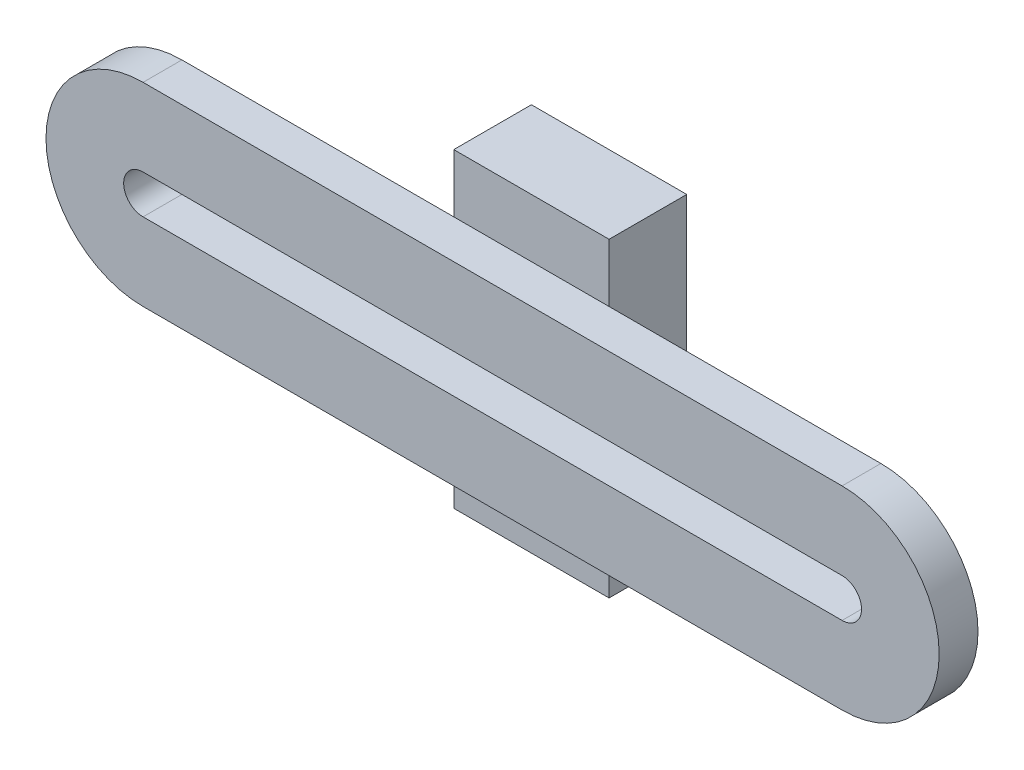
SolidWorks part; units mm, degrees
ref_plane "Front Plane" through (0, 0, 0) normal (0, 0, 1) x (1, 0, 0)
ref_plane "Top Plane" through (0, 0, 0) normal (0, 1, 0) x (1, 0, 0)
ref_plane "Right Plane" through (0, 0, 0) normal (1, 0, 0) x (0, 0, -1)
sketch "Sketch2" plane through (0, 0, 0) normal (0, 0, 1) x (1, 0, 0)
  line L0 (12.7, -571.3589) -> (12.7, 571.3589) construction
  line L1 (-12.7, -86.6057) -> (12.7, -86.6057)
  line L2 (-12.7, -86.6057) -> (-12.7, -35.8057)
  line L3 (-12.7, -35.8057) -> (12.7, -35.8057)
  line L4 (12.7, -86.6057) -> (12.7, -35.8057)
  line L5 (-12.7, -86.6057) -> (12.7, -35.8057) construction
  line L6 (-12.7, -35.8057) -> (12.7, -86.6057) construction
  circle A0 centre (0, -61.2057) radius 6.35 construction
  circle A1 centre (0, -61.2057) radius 6.35
  dimension "D1" = 50.8
extrude "Boss-Extrude1" add sketch "Sketch2" against normal up to surface (12.7 mm away)
sketch "Sketch3" plane through (0, 0, 0) normal (0, 0, 1) x (1, 0, 0)
  line L0 (-57.15, -61.2057) -> (57.15, -61.2057) construction
  line L1 (-57.15, -58.0307) -> (57.15, -58.0307)
  line L2 (-57.15, -64.3807) -> (57.15, -64.3807)
  line L3 (-57.15, -45.3307) -> (57.15, -45.3307)
  line L4 (-57.15, -77.0807) -> (57.15, -77.0807)
  arc A0 (-57.15, -58.0307) -> (-57.15, -64.3807) centre (-57.15, -61.2057) ccw
  arc A1 (57.15, -64.3807) -> (57.15, -58.0307) centre (57.15, -61.2057) ccw
  arc A2 (57.15, -77.0807) -> (57.15, -45.3307) centre (57.15, -61.2057) ccw
  arc A3 (-57.15, -45.3307) -> (-57.15, -77.0807) centre (-57.15, -61.2057) ccw
  point P2 (0, -61.2057)
  dimension "D1" = 114.3
  dimension "D2" = 6.35
  dimension "D3" = 12.7
extrude "Boss-Extrude2" add sketch "Sketch3" along normal blind 6.35
ref_plane "Plane4" through (0, -61.2057, 0) normal (0, 1, 0) x (1, 0, 0)
equation "\"D1@Sketch3\"=\"MaxSpinnerDiameter@ConceptAssem_2.Assembly\""
